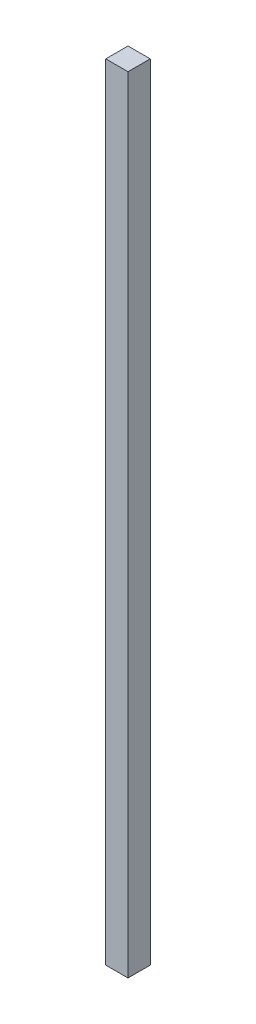
SolidWorks part; units mm, degrees
ref_plane "Спереди" through (0, 0, 0) normal (0, 0, 1) x (1, 0, 0)
ref_plane "Сверху" through (0, 0, 0) normal (0, 1, 0) x (1, 0, 0)
ref_plane "Справа" through (0, 0, 0) normal (1, 0, 0) x (0, 0, -1)
sketch "Эскиз1" plane through (0, 0, 0) normal (0, 1, 0) x (1, 0, 0)
  line L1 (-2.5, 2.5) -> (2.5, 2.5)
  line L2 (-2.5, 2.5) -> (-2.5, -2.5)
  line L3 (-2.5, -2.5) -> (2.5, -2.5)
  line L4 (2.5, 2.5) -> (2.5, -2.5)
  line L5 (-2.5, 2.5) -> (2.5, -2.5) construction
  line L6 (-2.5, -2.5) -> (2.5, 2.5) construction
  point P0 (0, 0)
extrude "Бобышка-Вытянуть1" add sketch "Эскиз1" along normal blind 176.37
sketch "Эскиз2" plane through (2.5, 0, 0) normal (1, 0, 0) x (0, 0, -1)
  line L0 (0, 0) -> (0, 176.37)
  line L1 (-2.5, 176.37) -> (2.5, 176.37) construction
  line L2 (-2.5, 0) -> (2.5, 0) construction
